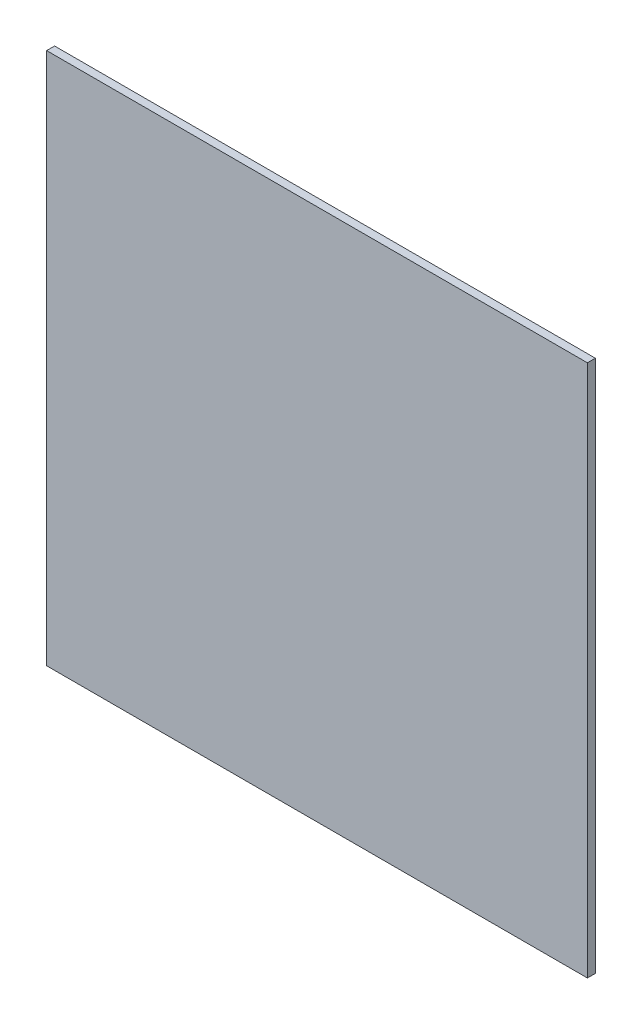
SolidWorks part; units mm, degrees
ref_plane "Plan de face" through (0, 0, 0) normal (0, 0, 1) x (1, 0, 0)
ref_plane "Plan de dessus" through (0, 0, 0) normal (0, 1, 0) x (1, 0, 0)
ref_plane "Plan de droite" through (0, 0, 0) normal (1, 0, 0) x (0, 0, -1)
sketch "Esquisse1" plane through (0, 0, 0) normal (0, 0, 1) x (1, 0, 0)
  line L1 (-340, 335) -> (340, 335)
  line L2 (-340, 335) -> (-340, -335)
  line L3 (-340, -335) -> (340, -335)
  line L4 (340, 335) -> (340, -335)
  dimension "D1" = 680
  dimension "D2" = 340
  dimension "D3" = 670
  dimension "D4" = 335
extrude "Boss.-Extru.1" add sketch "Esquisse1" along normal blind 10
